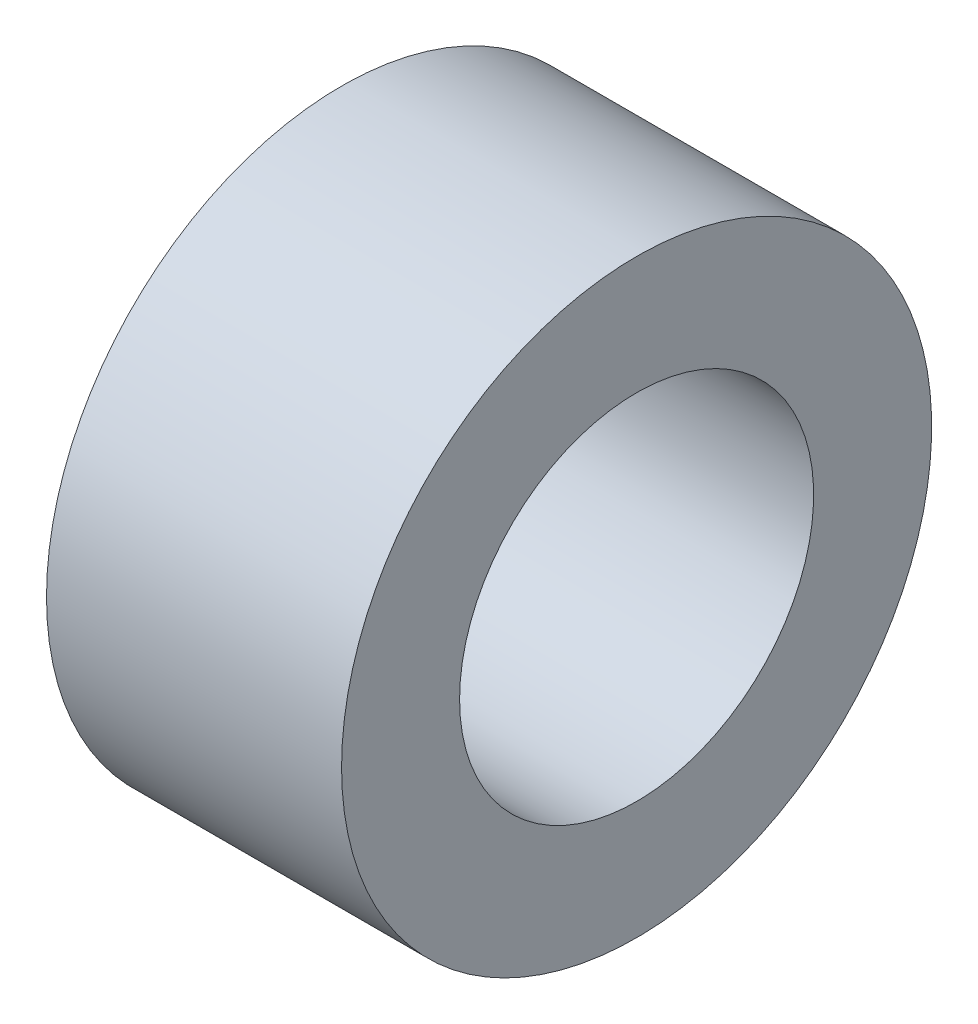
SolidWorks part; units mm, degrees
material "POM Acetal Copolymer"
ref_plane "Front Plane" through (0, 0, 0) normal (0, 0, 1) x (1, 0, 0)
ref_plane "Top Plane" through (0, 0, 0) normal (0, 1, 0) x (1, 0, 0)
ref_plane "Right Plane" through (0, 0, 0) normal (1, 0, 0) x (0, 0, -1)
sketch "Sketch1" plane through (0, 0, 0) normal (0, 0, 1) x (1, 0, 0)
  line L0 (-37.0032, 0) -> (2.5, 0) construction
  line L1 (-2.5, 5) -> (2.5, 5)
  line L2 (-2.5, 5) -> (-2.5, 3)
  line L3 (-2.5, 3) -> (2.5, 3)
  line L4 (2.5, 5) -> (2.5, 3)
  line L5 (2.5, 0) -> (2.5, 3) construction
  line L6 (0, 0) -> (0, 5) construction
  dimension "D1" = 6
  dimension "D2" = 5
  dimension "D3" = 10
revolve "Revolve1" add sketch "Sketch1" angle 360 about L0
